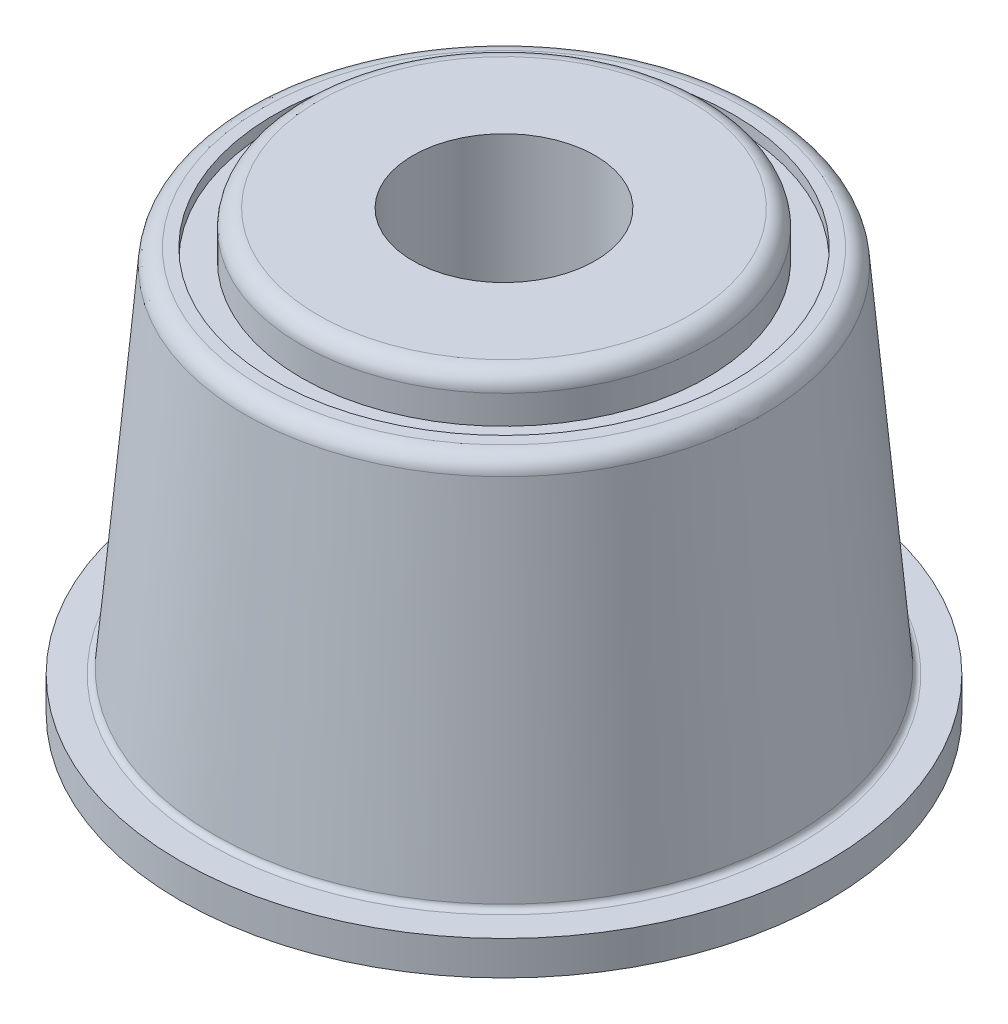
SolidWorks part; units mm, degrees
ref_plane "Front Plane" through (0, 0, 0) normal (0, 0, 1) x (1, 0, 0)
ref_plane "Top Plane" through (0, 0, 0) normal (0, 1, 0) x (1, 0, 0)
ref_plane "Right Plane" through (0, 0, 0) normal (1, 0, 0) x (0, 0, -1)
sketch "Sketch1" plane through (0, 0, 0) normal (0, 0, 1) x (1, 0, 0)
  line L0 (4.07, 9.6) -> (2, 9.6)
  line L1 (2, 9.6) -> (2, -0.75)
  line L2 (2, -0.75) -> (4.445, -0.75)
  line L3 (4.445, -0.75) -> (4.445, -0.125)
  line L4 (4.57, 0) -> (7.1, 0)
  line L5 (7.1, 0) -> (7.1, 0.75)
  line L6 (7.1, 0.75) -> (6.4645, 0.75)
  line L7 (6.34, 0.8641) -> (5.6713, 8.5077)
  line L8 (5.2977, 8.85) -> (5.0432, 8.85)
  line L9 (5.0432, 8.85) -> (5.0432, 8.6)
  line L10 (5.0432, 8.6) -> (4.445, 8.6)
  line L11 (4.445, 8.6) -> (4.445, 9.225)
  line L12 (0, 9.6027) -> (0, -0.75) construction
  arc A0 (4.445, -0.125) -> (4.57, 0) centre (4.57, -0.125) cw
  arc A1 (6.4645, 0.75) -> (6.34, 0.8641) centre (6.4645, 0.875) cw
  arc A2 (5.6713, 8.5077) -> (5.2977, 8.85) centre (5.2977, 8.475) ccw
  arc A3 (4.445, 9.225) -> (4.07, 9.6) centre (4.07, 9.225) ccw
revolve "Revolve1" add sketch "Sketch1" angle 360 about L12
